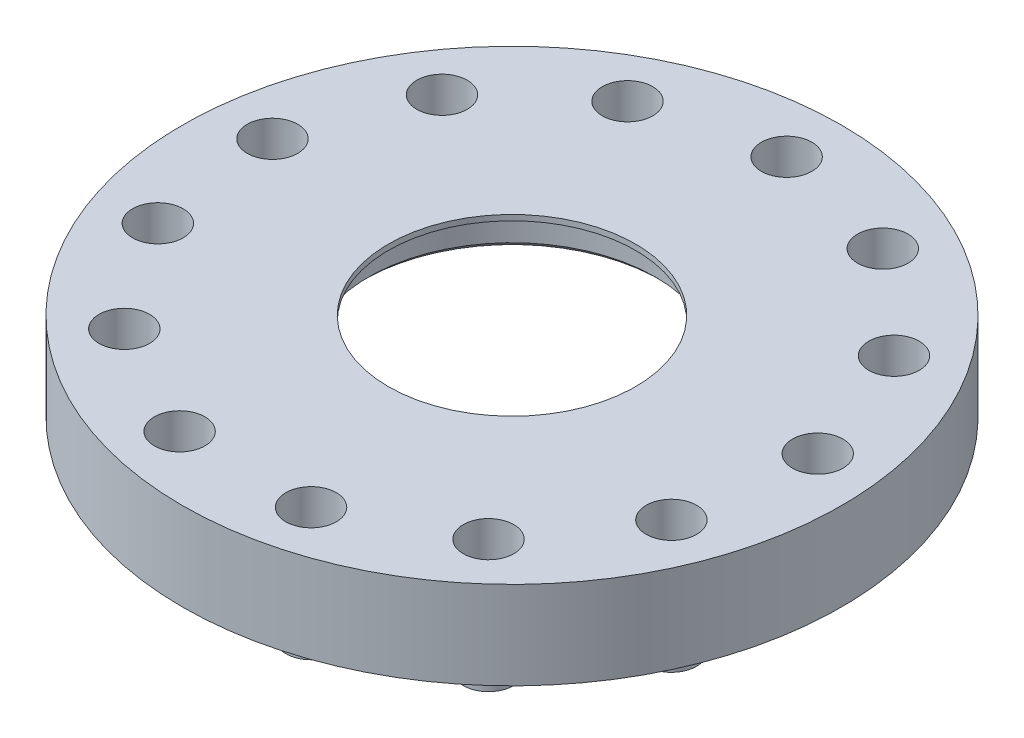
SolidWorks part; units mm, degrees
ref_plane "Front Plane" through (0, 0, 0) normal (0, 0, 1) x (1, 0, 0)
ref_plane "Top Plane" through (0, 0, 0) normal (0, 1, 0) x (1, 0, 0)
ref_plane "Right Plane" through (0, 0, 0) normal (1, 0, 0) x (0, 0, -1)
sketch "Sketch1" plane through (0, 0, 0) normal (0, 1, 0) x (1, 0, 0)
  circle A0 centre (0, 0) radius 60
  circle A1 centre (0, 0) radius 26.1
  circle A2 centre (0, 50) radius 2.6
  circle A3 centre (23.2362, 44.2728) radius 2.6
  circle A4 centre (41.1492, 28.4032) radius 2.6
  circle A5 centre (49.6354, 6.0268) radius 2.6
  circle A6 centre (46.7508, -17.7302) radius 2.6
  circle A7 centre (33.1561, -37.4255) radius 2.6
  circle A8 centre (11.9658, -48.5471) radius 2.6
  circle A9 centre (-11.9658, -48.5471) radius 2.6
  circle A10 centre (-33.1561, -37.4255) radius 2.6
  circle A11 centre (-46.7508, -17.7302) radius 2.6
  circle A12 centre (-49.6354, 6.0268) radius 2.6
  circle A13 centre (-41.1492, 28.4032) radius 2.6
  circle A14 centre (-23.2362, 44.2728) radius 2.6
  point P32 (0, 0)
  dimension "D1" = 120
  dimension "D2" = 52.2
  dimension "D3" = 5.2
  dimension "D4" = 50
  dimension "D5" = 13
extrude "Boss-Extrude1" add sketch "Sketch1" along normal blind 8
sketch "Sketch2" plane through (0, 0, 0) normal (0, -1, 0) x (-1, 0, 0)
  circle A0 centre (0, 0) radius 40
  circle A1 centre (0, 0) radius 60 construction
  circle A2 centre (23.2362, 44.2728) radius 2.6
  circle A3 centre (23.2362, 44.2728) radius 2.6
  circle A4 centre (41.1492, 28.4032) radius 2.6
  circle A5 centre (41.1492, 28.4032) radius 2.6
  circle A6 centre (49.6354, 6.0268) radius 2.6
  circle A7 centre (49.6354, 6.0268) radius 2.6
  circle A8 centre (46.7508, -17.7302) radius 2.6
  circle A9 centre (46.7508, -17.7302) radius 2.6
  circle A10 centre (33.1561, -37.4255) radius 2.6
  circle A11 centre (33.1561, -37.4255) radius 2.6
  circle A12 centre (11.9658, -48.5471) radius 2.6
  circle A13 centre (11.9658, -48.5471) radius 2.6
  circle A14 centre (-11.9658, -48.5471) radius 2.6
  circle A15 centre (-11.9658, -48.5471) radius 2.6
  circle A16 centre (-33.1561, -37.4255) radius 2.6
  circle A17 centre (-33.1561, -37.4255) radius 2.6
  circle A18 centre (-46.7508, -17.7302) radius 2.6
  circle A19 centre (-46.7508, -17.7302) radius 2.6
  circle A20 centre (-49.6354, 6.0268) radius 2.6
  circle A21 centre (-49.6354, 6.0268) radius 2.6
  circle A22 centre (-41.1492, 28.4032) radius 2.6
  circle A23 centre (-41.1492, 28.4032) radius 2.6
  circle A24 centre (-23.2362, 44.2728) radius 2.6
  circle A25 centre (-23.2362, 44.2728) radius 2.6
  circle A26 centre (0, 50) radius 2.6
  circle A27 centre (0, 50) radius 2.6
  circle A28 centre (0, 0) radius 60
  dimension "D14" = 80
  dimension "D1" = 0
  dimension "D2" = 0
  dimension "D3" = 0
  dimension "D4" = 0
  dimension "D5" = 0
  dimension "D6" = 0
  dimension "D7" = 0
  dimension "D8" = 0
  dimension "D9" = 0
  dimension "D10" = 0
  dimension "D11" = 0
  dimension "D12" = 0
  dimension "D13" = 0
extrude "Boss-Extrude2" add sketch "Sketch2" along normal blind 8
sketch "Sketch3" plane through (0, -8, 0) normal (0, -1, 0) x (1, 0, 0)
  circle A0 centre (0, -50) radius 4.6
  circle A1 centre (0, -50) radius 2.6
  circle A2 centre (0, -50) radius 2.6
  circle A3 centre (41.1492, -28.4032) radius 2.6
  circle A4 centre (41.1492, -28.4032) radius 2.6
  circle A5 centre (46.7508, 17.7302) radius 2.6
  circle A6 centre (46.7508, 17.7302) radius 2.6
  circle A7 centre (11.9658, 48.5471) radius 2.6
  circle A8 centre (11.9658, 48.5471) radius 2.6
  circle A9 centre (-33.1561, 37.4255) radius 2.6
  circle A10 centre (-33.1561, 37.4255) radius 2.6
  circle A11 centre (-49.6354, -6.0268) radius 2.6
  circle A12 centre (-49.6354, -6.0268) radius 2.6
  circle A13 centre (-23.2362, -44.2728) radius 2.6
  circle A14 centre (-23.2362, -44.2728) radius 2.6
  circle A15 centre (-41.1492, -28.4032) radius 2.6
  circle A16 centre (-41.1492, -28.4032) radius 2.6
  circle A17 centre (-46.7508, 17.7302) radius 2.6
  circle A18 centre (-46.7508, 17.7302) radius 2.6
  circle A19 centre (-11.9658, 48.5471) radius 2.6
  circle A20 centre (-11.9658, 48.5471) radius 2.6
  circle A21 centre (33.1561, 37.4255) radius 2.6
  circle A22 centre (33.1561, 37.4255) radius 2.6
  circle A23 centre (49.6354, -6.0268) radius 2.6
  circle A24 centre (49.6354, -6.0268) radius 2.6
  circle A25 centre (23.2362, -44.2728) radius 2.6
  circle A26 centre (23.2362, -44.2728) radius 2.6
  circle A27 centre (41.1492, -28.4032) radius 4.6
  circle A28 centre (46.7508, 17.7302) radius 4.6
  circle A29 centre (11.9658, 48.5471) radius 4.6
  circle A30 centre (-33.1561, 37.4255) radius 4.6
  circle A31 centre (-49.6354, -6.0268) radius 4.6
  circle A32 centre (-23.2362, -44.2728) radius 4.6
  circle A33 centre (-41.1492, -28.4032) radius 4.6
  circle A34 centre (-46.7508, 17.7302) radius 4.6
  circle A35 centre (-11.9658, 48.5471) radius 4.6
  circle A36 centre (33.1561, 37.4255) radius 4.6
  circle A37 centre (49.6354, -6.0268) radius 4.6
  circle A38 centre (23.2362, -44.2728) radius 4.6
  dimension "D1" = 0
  dimension "D2" = 0
  dimension "D3" = 0
  dimension "D4" = 0
  dimension "D5" = 0
  dimension "D6" = 0
  dimension "D7" = 0
  dimension "D8" = 0
  dimension "D9" = 0
  dimension "D10" = 0
  dimension "D11" = 0
  dimension "D12" = 0
  dimension "D13" = 0
  dimension "D14" = 2
extrude "Boss-Extrude3" add sketch "Sketch3" along normal blind 4.8
sketch "Sketch4" plane through (0, 8, 0) normal (0, 1, 0) x (1, 0, 0)
  circle A0 centre (0, 0) radius 22.5
  circle A2 centre (0, 0) radius 26.1
  circle A3 centre (0, 0) radius 26.1
  dimension "D1" = 45
  dimension "D2" = 0
extrude "Boss-Extrude4" add sketch "Sketch4" against normal blind 1
chamfer "Chamfer1" distance 1 angle 45 1 edges at (0, 0, 26.1)
sketch "Sketch5" plane through (0, 8, 0) normal (0, 1, 0) x (1, 0, 0)
  circle A0 centre (-23.2362, 44.2728) radius 4.6
  circle A1 centre (-23.2362, 44.2728) radius 2.6
  circle A2 centre (-23.2362, 44.2728) radius 2.6
  circle A3 centre (-49.6354, 6.0268) radius 2.6
  circle A4 centre (-49.6354, 6.0268) radius 2.6
  circle A5 centre (-33.1561, -37.4255) radius 2.6
  circle A6 centre (-33.1561, -37.4255) radius 2.6
  circle A7 centre (11.9658, -48.5471) radius 2.6
  circle A8 centre (11.9658, -48.5471) radius 2.6
  circle A9 centre (46.7508, -17.7302) radius 2.6
  circle A10 centre (46.7508, -17.7302) radius 2.6
  circle A11 centre (41.1492, 28.4032) radius 2.6
  circle A12 centre (41.1492, 28.4032) radius 2.6
  circle A13 centre (0, 50) radius 2.6
  circle A14 centre (0, 50) radius 2.6
  circle A15 centre (23.2362, 44.2728) radius 2.6
  circle A16 centre (23.2362, 44.2728) radius 2.6
  circle A17 centre (49.6354, 6.0268) radius 2.6
  circle A18 centre (49.6354, 6.0268) radius 2.6
  circle A19 centre (33.1561, -37.4255) radius 2.6
  circle A20 centre (33.1561, -37.4255) radius 2.6
  circle A21 centre (-11.9658, -48.5471) radius 2.6
  circle A22 centre (-11.9658, -48.5471) radius 2.6
  circle A23 centre (-46.7508, -17.7302) radius 2.6
  circle A24 centre (-46.7508, -17.7302) radius 2.6
  circle A25 centre (-41.1492, 28.4032) radius 2.6
  circle A26 centre (-41.1492, 28.4032) radius 2.6
  circle A27 centre (-49.6354, 6.0268) radius 4.6
  circle A28 centre (-33.1561, -37.4255) radius 4.6
  circle A29 centre (11.9658, -48.5471) radius 4.6
  circle A30 centre (46.7508, -17.7302) radius 4.6
  circle A31 centre (41.1492, 28.4032) radius 4.6
  circle A32 centre (0, 50) radius 4.6
  circle A33 centre (23.2362, 44.2728) radius 4.6
  circle A34 centre (49.6354, 6.0268) radius 4.6
  circle A35 centre (33.1561, -37.4255) radius 4.6
  circle A36 centre (-11.9658, -48.5471) radius 4.6
  circle A37 centre (-46.7508, -17.7302) radius 4.6
  circle A38 centre (-41.1492, 28.4032) radius 4.6
  dimension "D1" = 0
  dimension "D2" = 0
  dimension "D3" = 0
  dimension "D4" = 0
  dimension "D5" = 0
  dimension "D6" = 0
  dimension "D7" = 0
  dimension "D8" = 0
  dimension "D9" = 0
  dimension "D10" = 0
  dimension "D11" = 0
  dimension "D12" = 0
  dimension "D13" = 0
  dimension "D14" = 2
extrude "Cut-Extrude1" cut sketch "Sketch5" against normal blind 7
